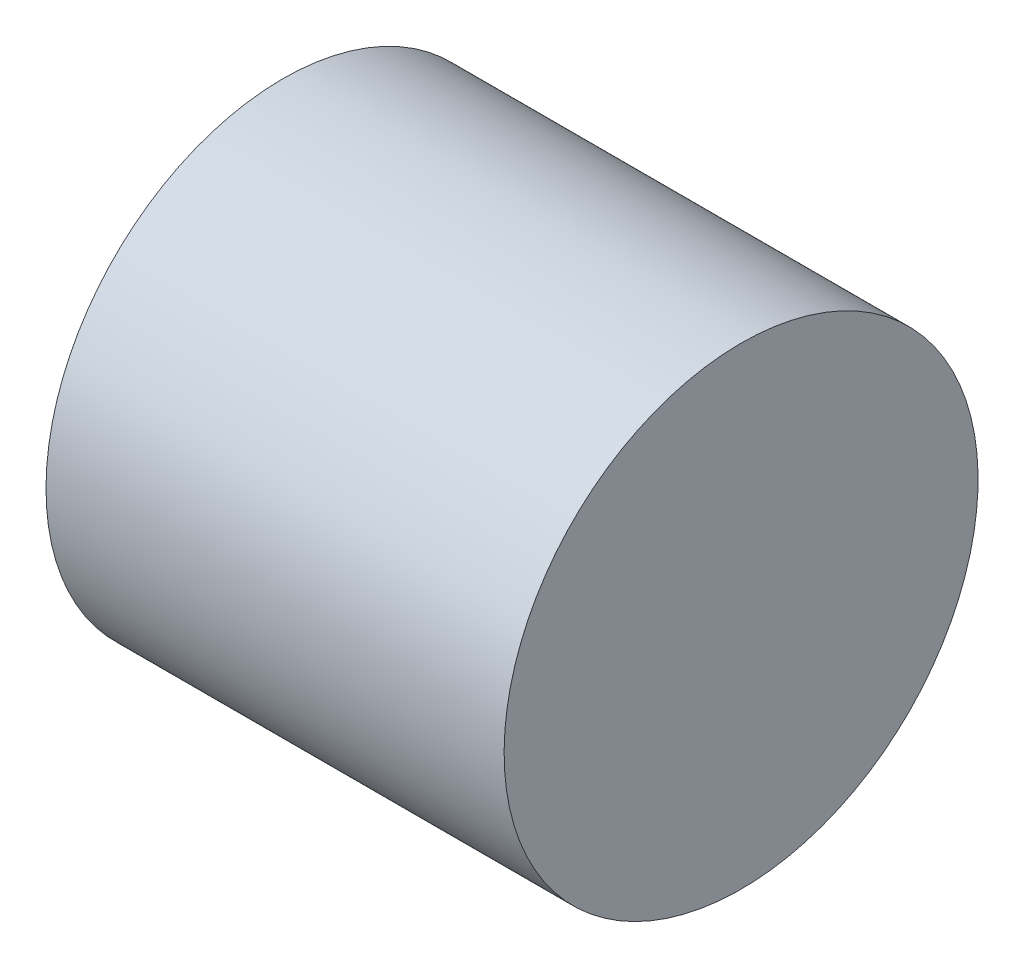
SolidWorks part; units mm, degrees
ref_plane "Front Plane" through (0, 0, 0) normal (0, 0, 1) x (1, 0, 0)
ref_plane "Top Plane" through (0, 0, 0) normal (0, 1, 0) x (1, 0, 0)
ref_plane "Right Plane" through (0, 0, 0) normal (1, 0, 0) x (0, 0, -1)
sketch "Sketch1" plane through (0, 0, 0) normal (1, 0, 0) x (0, 0, -1)
  ellipse E0 centre (0, 0) end of major axis (45.9736, 1.0946) minor radius 45.8911
extrude "Boss-Extrude1" add sketch "Sketch1" along normal blind 88.9
